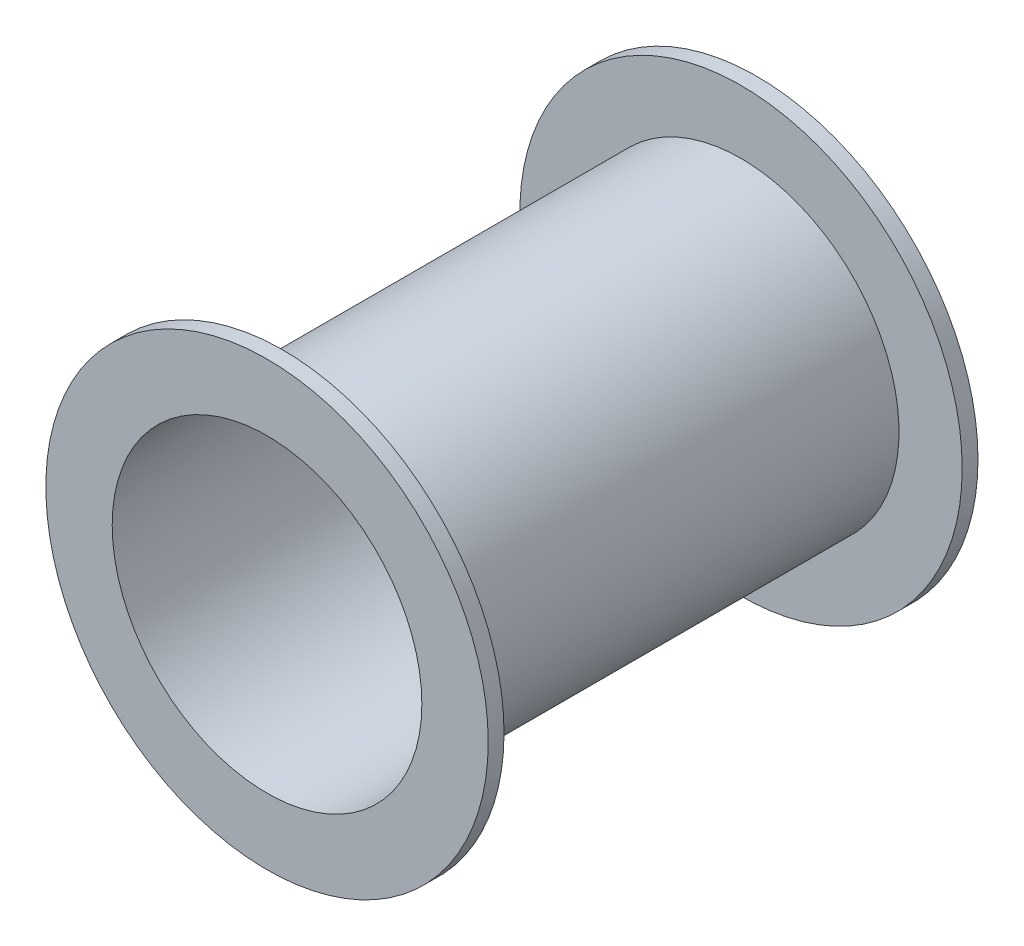
SolidWorks part; units mm, degrees
ref_plane "Front Plane" through (0, 0, 0) normal (0, 0, 1) x (1, 0, 0)
ref_plane "Top Plane" through (0, 0, 0) normal (0, 1, 0) x (1, 0, 0)
ref_plane "Right Plane" through (0, 0, 0) normal (1, 0, 0) x (0, 0, -1)
sketch "Sketch2" plane through (0, 0, 0) normal (0, 0, 1) x (1, 0, 0)
  circle A0 centre (0, 0) radius 100
  dimension "D1" = 200
extrude "Extrude-Thin1" add sketch "Sketch2" along normal blind 310 thin thin type one direction reverse wall 2
sketch "Sketch3" plane through (0, 0, 310) normal (0, 0, 1) x (1, 0, 0)
  circle A0 centre (0, 0) radius 140
  circle A1 centre (0, 0) radius 100
  circle A2 centre (0, 0) radius 100
  dimension "D2" = 280
  dimension "D1" = 0
extrude "Boss-Extrude1" add sketch "Sketch3" against normal blind 10
ref_plane "Plane1" through (0, 0, 155) normal (0, 0, 1) x (1, 0, 0)
mirror "Mirror1" about plane through (0, 0, 155) normal (0, 0, 1) of "Boss-Extrude1"
